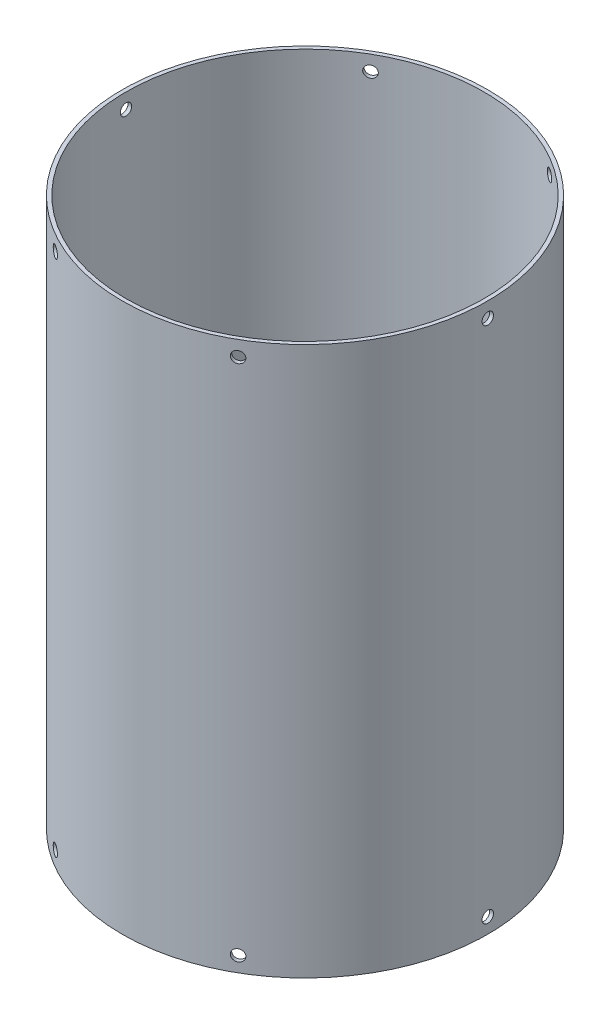
SolidWorks part; units mm, degrees
material "Hexcel AS4C (3000 Filaments)"
ref_plane "Front Plane" through (0, 0, 0) normal (0, 0, 1) x (1, 0, 0)
ref_plane "Top Plane" through (0, 0, 0) normal (0, 1, 0) x (1, 0, 0)
ref_plane "Right Plane" through (0, 0, 0) normal (1, 0, 0) x (0, 0, -1)
sketch "Sketch1" plane through (0, 0, 0) normal (0, 1, 0) x (1, 0, 0)
  circle A0 centre (0, 0) radius 152.4
  circle A1 centre (0, 0) radius 149.225
  dimension "D1" = 304.8
  dimension "D2" = 298.45
extrude "Boss-Extrude1" add sketch "Sketch1" along normal blind 457.2
ref_plane "Plane1" through (-152.4, 0, 0) normal (-1, 0, 0) x (0, 0, 1)
hole_wizard "3/8 (0.375) Diameter Hole1" positions "Sketch2" profile "Sketch3" hole size "3/8" standard "ANSI Inch"
sketch "Sketch2" plane through (-152.4, 0, 0) normal (-1, 0, 0) x (0, 0, 1)
  line L0 (0, -167.64) -> (0, 167.64) construction
  line L1 (149.225, 457.2) -> (-149.225, 457.2) construction
  point P0 (0, 444.5)
  dimension "D1" = 12.7
sketch "Sketch3" plane through (-152.4, 444.5, 0) normal (0, 1, 0) x (0, 0, 1)
  line L0 (0, 0) -> (0, 356.2465)
  line L1 (0, 356.2465) -> (4.7625, 356.2465)
  line L2 (4.7625, 356.2465) -> (4.7625, 0)
  line L5 (4.7625, 0) -> (0, 0)
  line L11 (0, -6.35) -> (0, 107.95) construction
  dimension "Thru Hole Dia." = 9.525
  dimension "Thru Hole Depth" = 356.2465
pattern_circular "CirPattern1" count 6 over 360 about axis through (0, 457.2, 0) along (0, -1, 0) of "3/8 (0.375) Diameter Hole1"
ref_plane "Plane2" through (0, 228.6, 0) normal (0, 1, 0) x (1, 0, 0)
mirror "Mirror1" about plane through (0, 228.6, 0) normal (0, 1, 0) of "CirPattern1", "3/8 (0.375) Diameter Hole1"
